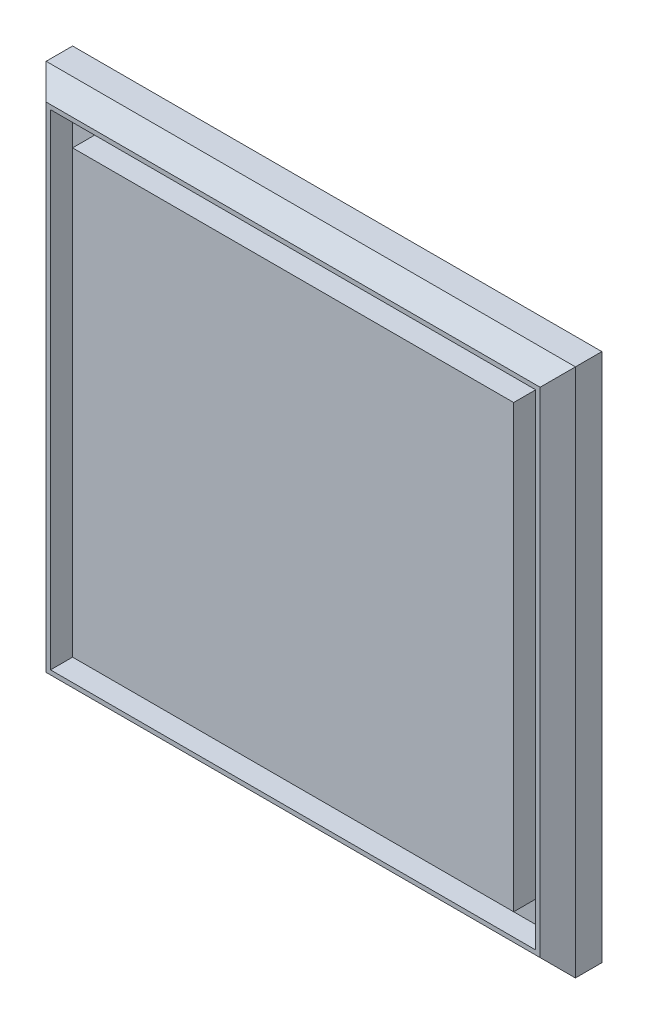
SolidWorks part; units mm, degrees
ref_plane "Спереди" through (0, 0, 0) normal (0, 0, 1) x (1, 0, 0)
ref_plane "Сверху" through (0, 0, 0) normal (0, 1, 0) x (1, 0, 0)
ref_plane "Справа" through (0, 0, 0) normal (1, 0, 0) x (0, 0, -1)
sketch "Эскиз1" plane through (0, 0, 0) normal (0, 0, 1) x (1, 0, 0)
  line L1 (-120, 120) -> (120, 120)
  line L2 (-120, 120) -> (-120, -120)
  line L3 (-120, -120) -> (120, -120)
  line L4 (120, 120) -> (120, -120)
  line L5 (-120, 120) -> (120, -120) construction
  line L6 (-120, -120) -> (120, 120) construction
  point P0 (0, 0)
  dimension "D1" = 240
extrude "Бобышка-Вытянуть1" add sketch "Эскиз1" along normal blind 20 contours L2 L3 L4 L1
chamfer "Фаска1" distance 8 angle 45 4 edges at (120, 0, 20) (0, -120, 20) (-120, 0, 20) (0, 120, 20)
sketch "Эскиз2" plane through (0, 0, 20) normal (0, 0, 1) x (1, 0, 0)
  line L0 (120, 120) -> (120, -120) construction
  line L1 (110, -110) -> (-110, -110)
  line L2 (110, -110) -> (110, 110)
  line L3 (110, 110) -> (-110, 110)
  line L4 (-110, -110) -> (-110, 110)
  line L5 (110, -110) -> (-110, 110) construction
  line L6 (110, 110) -> (-110, -110) construction
  line L8 (100, -100) -> (-100, -100)
  line L9 (100, -100) -> (100, 100)
  line L10 (100, 100) -> (-100, 100)
  line L11 (-100, -100) -> (-100, 100)
  line L12 (100, -100) -> (-100, 100) construction
  line L13 (100, 100) -> (-100, -100) construction
  point P0 (0, 0)
  point P8 (0, 0)
  dimension "D1" = 10
  dimension "D2" = 10
extrude "Вырез-Вытянуть1" cut sketch "Эскиз2" against normal blind 10
